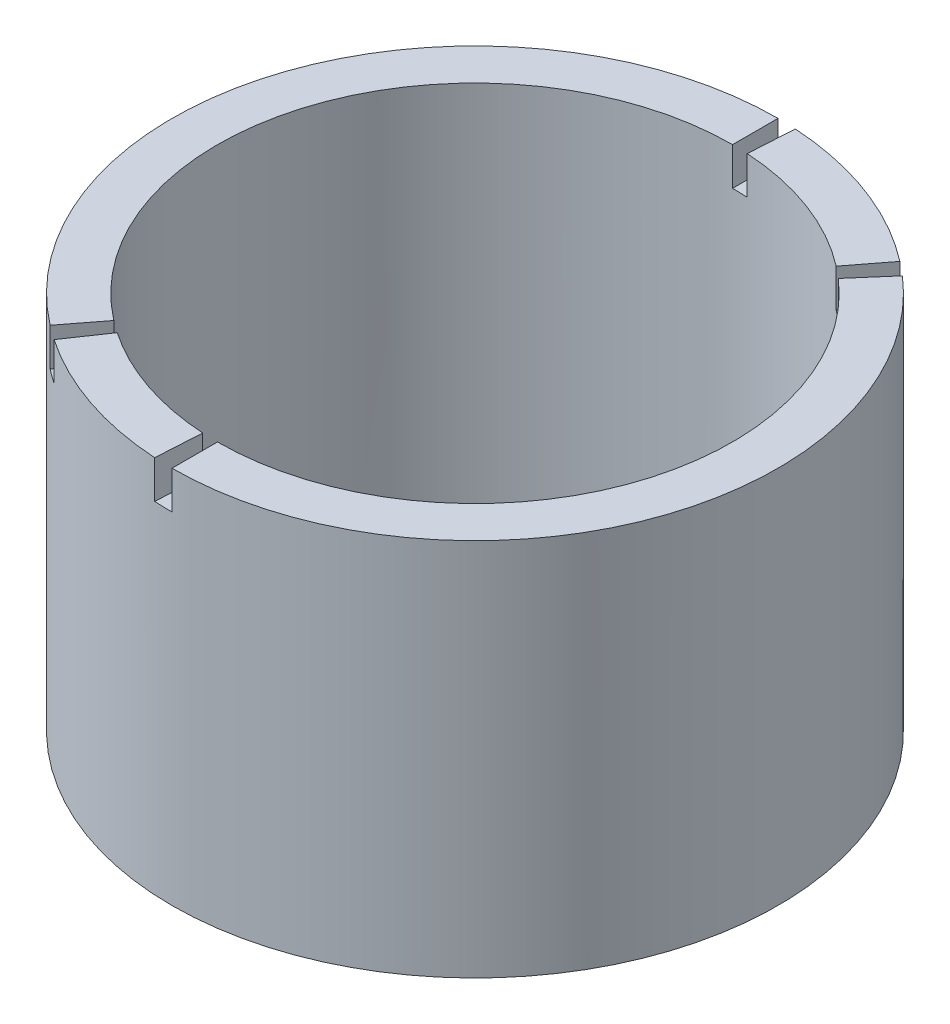
SolidWorks part; units mm, degrees
ref_plane "Plan de face" through (0, 0, 0) normal (0, 0, 1) x (1, 0, 0)
ref_plane "Plan de dessus" through (0, 0, 0) normal (0, 1, 0) x (1, 0, 0)
ref_plane "Plan de droite" through (0, 0, 0) normal (1, 0, 0) x (0, 0, -1)
sketch "Esquisse1" plane through (0, 0, 0) normal (0, 1, 0) x (1, 0, 0)
  circle A0 centre (0, 0) radius 40
  circle A1 centre (0, 0) radius 34
  dimension "D1" = 80
  dimension "D2" = 6
extrude "Extrusion1" add sketch "Esquisse1" along normal blind 50
sketch "Esquisse2" plane through (0, 50, 0) normal (0, 1, 0) x (1, 0, 0)
  line L0 (0, 0) -> (0, 40) construction
  line L1 (0, 0) -> (0, -40) construction
  line L2 (0, -40) -> (0, -34)
  line L3 (0, 40) -> (0, 34)
  line L4 (0, 0) -> (2.3529, 39.9307) construction
  line L5 (0, 0) -> (-2.3529, -39.9307) construction
  line L6 (-2.3529, -39.9307) -> (-2, -33.9411)
  line L7 (2.3529, 39.9307) -> (2, 33.9411)
  line L8 (0, 0) -> (24.3956, 31.6994) construction
  line L9 (24.3956, 31.6994) -> (20.7363, 26.9445)
  line L10 (0, 0) -> (26.2173, 30.2102) construction
  line L11 (26.2173, 30.2102) -> (22.2847, 25.6787)
  line L12 (0, 0) -> (-22.4895, -33.079) construction
  line L13 (-22.4895, -33.079) -> (-19.1161, -28.1172)
  line L14 (0, 0) -> (-24.3956, -31.6994) construction
  line L15 (-24.3956, -31.6994) -> (-20.7363, -26.9445)
  circle A0 centre (0, 0) radius 40 construction
  circle A1 centre (0, 0) radius 34 construction
  arc A2 (0, 40) -> (2.3529, 39.9307) centre (0, 0) cw
  arc A3 (0, 34) -> (2, 33.9411) centre (0, 0) cw
  arc A4 (-2, -33.9411) -> (0, -34) centre (0, 0) ccw
  arc A5 (-2.3529, -39.9307) -> (0, -40) centre (0, 0) ccw
  arc A6 (24.3956, 31.6994) -> (26.2173, 30.2102) centre (0, 0) cw
  arc A7 (20.7363, 26.9445) -> (22.2847, 25.6787) centre (0, 0) cw
  circle A8 centre (0, 0) radius 40 construction
  circle A9 centre (0, 0) radius 34 construction
  arc A10 (-22.4895, -33.079) -> (-24.3956, -31.6994) centre (0, 0) cw
  arc A11 (-19.1161, -28.1172) -> (-20.7363, -26.9445) centre (0, 0) cw
  circle A12 centre (0, 0) radius 40 construction
  circle A13 centre (0, 0) radius 34 construction
  dimension "D1" = 2
  dimension "D2" = 2
  dimension "D3" = 20
  dimension "D4" = 2
extrude "Extrusion2" cut sketch "Esquisse2" against normal blind 5
